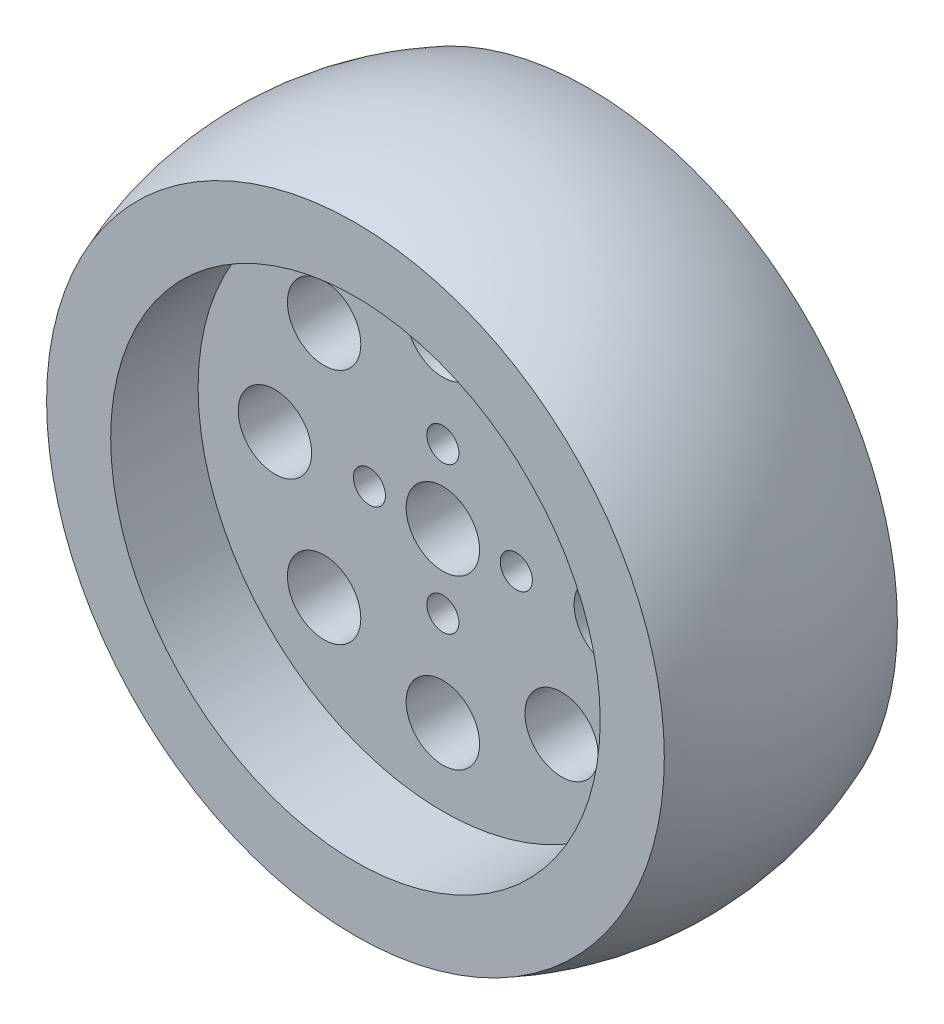
SolidWorks part; units mm, degrees
material "Nylon"
ref_plane "Front Plane" through (0, 0, 0) normal (0, 0, 1) x (1, 0, 0)
ref_plane "Top Plane" through (0, 0, 0) normal (0, 1, 0) x (1, 0, 0)
ref_plane "Right Plane" through (0, 0, 0) normal (1, 0, 0) x (0, 0, -1)
sketch "Sketch1" plane through (0, 0, 0) normal (0, 0, 1) x (1, 0, 0)
  circle A0 centre (0, 0) radius 31.75
  dimension "D1" = 63.5
extrude "Extrude1" add sketch "Sketch1" against normal blind 21.082
sketch "Sketch2" plane through (0, 0, 0) normal (0, 0, 1) x (1, 0, 0)
  circle A0 centre (0, 0) radius 26.67
  dimension "D1" = 53.34
extrude "Cut-Extrude1" cut sketch "Sketch2" against normal blind 7.366
sketch "Sketch3" plane through (0, 0, -21.082) normal (0, 0, -1) x (-1, 0, 0)
  circle A0 centre (0, 0) radius 26.67
  dimension "D1" = 53.34
extrude "Cut-Extrude2" cut sketch "Sketch3" against normal blind 7.366
sketch "Sketch5" plane through (0, 0, 0) normal (0, 0, 1) x (1, 0, 0)
  circle A0 centre (0, 0) radius 33.655
  dimension "D1" = 67.31
extrude "Extrude3" add sketch "Sketch5" along normal blind 2.159
sketch "Sketch6" plane through (0, 0, 2.159) normal (0, 0, 1) x (1, 0, 0)
  circle A0 centre (0, 0) radius 26.67
  dimension "D1" = 53.34
extrude "Cut-Extrude3" cut sketch "Sketch6" against normal up to next
sketch "Sketch7" plane through (0, 0, -21.082) normal (0, 0, -1) x (-1, 0, 0)
  circle A0 centre (0, 0) radius 33.655
  dimension "D1" = 67.31
extrude "Extrude4" add sketch "Sketch7" along normal blind 2.159
sketch "Sketch8" plane through (0, 0, -23.241) normal (0, 0, -1) x (-1, 0, 0)
  circle A0 centre (0, 0) radius 26.67
  dimension "D1" = 53.34
extrude "Cut-Extrude4" cut sketch "Sketch8" against normal up to next
sketch3d "3DSketch2"
  line L0 (0, 33.655, 2.159) -> (0, 33.655, 0)
  line L1 (0, 33.655, 0) -> (0, 31.75, 0)
  line L2 (0, 31.75, 0) -> (0, 31.75, -21.082)
  line L3 (0, 31.75, -21.082) -> (0, 33.655, -21.082)
  line L4 (0, 33.655, -21.082) -> (0, 33.655, -23.241)
  circle A0 centre (0, 0, 2.159) radius 33.655 construction
  arc A1 (0, 33.655, 2.159) -> (0, 33.655, -23.241) centre (0, 1.8775, -10.541) cw
  circle A2 centre (0, 0, -23.241) radius 33.655 construction
  circle A3 centre (0, 0, 0) radius 33.655 construction
  circle A4 centre (0, 0, 0) radius 31.75 construction
  circle A5 centre (0, 0, -21.082) radius 31.75 construction
  circle A6 centre (0, 0, -21.082) radius 33.655 construction
  point P2 (0, 0, 35.814)
  point P5 (-34.2214, 1.8775, -10.541)
  point P10 (0, 0, -56.896)
  point P13 (0, 0, 33.655)
  point P17 (0, 0, 31.75)
  point P21 (0, 0, 10.668)
  point P25 (0, 0, -54.737)
sweep "Sweep2" add profiles "3DSketch2" path edge at (33.655, 0, 2.159)
sketch "Sketch10" plane through (0, 0, -7.366) normal (0, 0, 1) x (1, 0, 0)
  circle A0 centre (0, 0) radius 4
  circle A1 centre (0, 8) radius 1.75
  circle A2 centre (8, 0) radius 1.75
  circle A3 centre (0, -8) radius 1.75
  circle A4 centre (-8, 0) radius 1.75
  dimension "D1" = 8
  dimension "D2" = 3.5
  dimension "D3" = 3.5
  dimension "D4" = 3.5
  dimension "D5" = 3.5
  dimension "D6" = 8
  dimension "D7" = 8
  dimension "D8" = 8
  dimension "D9" = 8
extrude "Cut-Extrude5" cut sketch "Sketch10" against normal through all
sketch "Sketch11" plane through (0, 0, -7.366) normal (0, 0, 1) x (1, 0, 0)
  circle A0 centre (0, 18.3) radius 4
  circle A1 centre (18.3, 0) radius 4
  circle A2 centre (0, -18.3) radius 4
  circle A3 centre (-18.3, 0) radius 4
  dimension "D1" = 8
  dimension "D2" = 8
  dimension "D3" = 8
  dimension "D4" = 8
  dimension "D5" = 18.3
  dimension "D6" = 18.3
  dimension "D7" = 18.3
  dimension "D8" = 18.3
extrude "Cut-Extrude6" cut sketch "Sketch11" against normal through all
sketch "Sketch12" plane through (0, 0, -7.366) normal (0, 0, 1) x (1, 0, 0)
  line L0 (0, 0) -> (31.6986, 31.6986) construction
  line L1 (0, 0) -> (-32.9498, -32.9498) construction
  line L2 (0, 0) -> (35.3133, -35.3133) construction
  line L3 (0, 0) -> (-31.5595, 31.5595) construction
  circle A0 centre (12.9401, 12.9401) radius 4
  circle A1 centre (12.9401, -12.9401) radius 4
  circle A2 centre (-12.9401, -12.9401) radius 4
  circle A3 centre (-12.9401, 12.9401) radius 4
  dimension "D1" = 8
  dimension "D2" = 8
  dimension "D3" = 8
  dimension "D4" = 8
  dimension "D5" = 18.3
  dimension "D6" = 18.3
  dimension "D7" = 18.3
  dimension "D8" = 18.3
extrude "Cut-Extrude7" cut sketch "Sketch12" against normal through all
